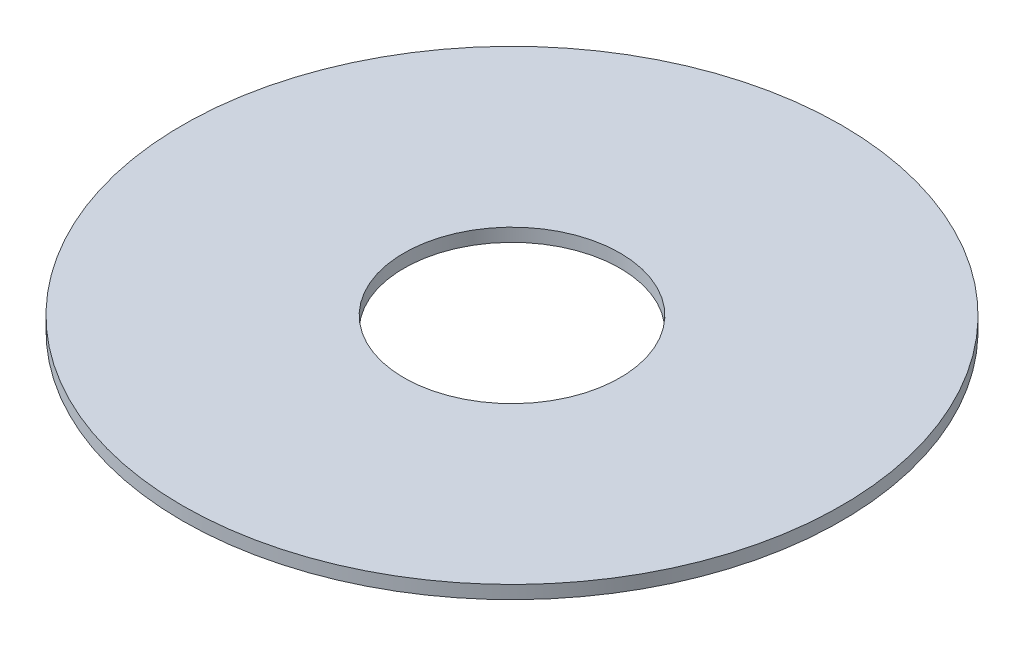
SolidWorks part; units mm, degrees
ref_plane "Front Plane" through (0, 0, 0) normal (0, 0, 1) x (1, 0, 0)
ref_plane "Top Plane" through (0, 0, 0) normal (0, 1, 0) x (1, 0, 0)
ref_plane "Right Plane" through (0, 0, 0) normal (1, 0, 0) x (0, 0, -1)
sketch "Sketch1" plane through (0, 0, 0) normal (0, 1, 0) x (1, 0, 0)
  circle A0 centre (0, 0) radius 63.5
  circle A1 centre (0, 0) radius 20.828
  dimension "D1" = 127
  dimension "D2" = 41.656
extrude "Boss-Extrude1" add sketch "Sketch1" along normal blind 2.54
